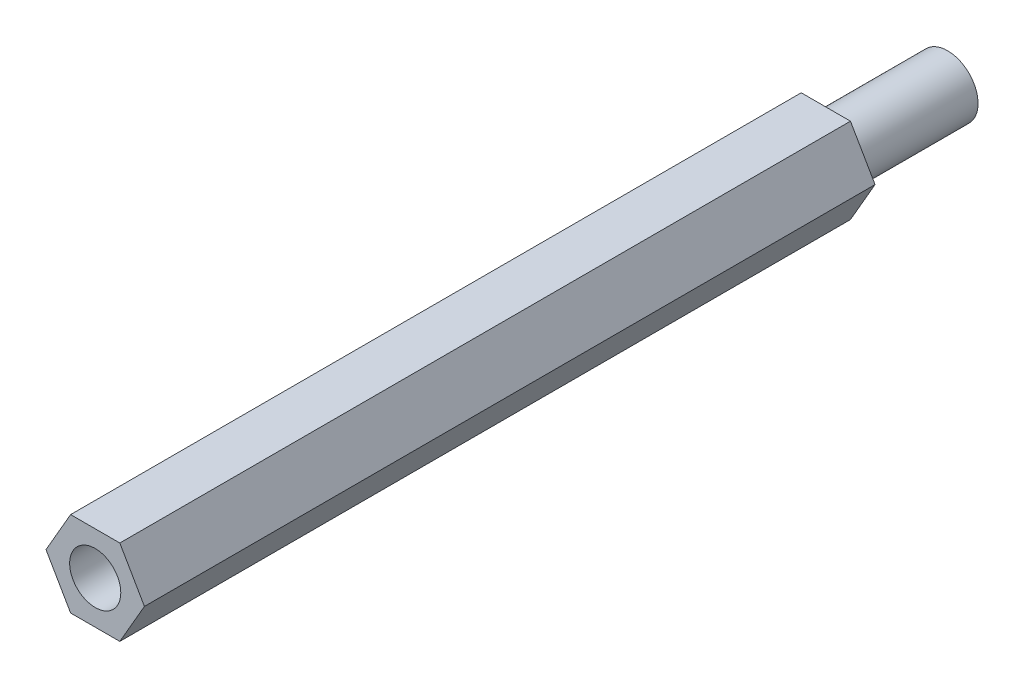
SolidWorks part; units mm, degrees
material "黃銅"
ref_plane "前基準面" through (0, 0, 0) normal (0, 0, 1) x (1, 0, 0)
ref_plane "上基準面" through (0, 0, 0) normal (0, 1, 0) x (1, 0, 0)
ref_plane "右基準面" through (0, 0, 0) normal (1, 0, 0) x (0, 0, -1)
sketch "草圖1" plane through (0, 0, 0) normal (0, 0, 1) x (1, 0, 0)
  line L1 (-2.0207, 3.5) -> (-4.0415, 0)
  line L2 (-4.0415, 0) -> (-2.0207, -3.5)
  line L3 (-2.0207, -3.5) -> (2.0207, -3.5)
  line L4 (2.0207, -3.5) -> (4.0415, 0)
  line L5 (4.0415, 0) -> (2.0207, 3.5)
  line L6 (2.0207, 3.5) -> (-2.0207, 3.5)
  circle A0 centre (0, 0) radius 3.5 construction
  dimension "D1" = 7
extrude "填料-伸長1" add sketch "草圖1" along normal blind 60
sketch "草圖4" plane through (0, 0, 0) normal (0, 0, -1) x (-1, 0, 0)
  circle A0 centre (0, 0) radius 2.5
  dimension "D1" = 5
extrude "填料-伸長2" add sketch "草圖4" along normal blind 10
hole_wizard "M5x0.8 Tapped Hole1" positions "草圖2" profile "草圖3" tap size "M5x0.8" standard "ANSI Metric"
sketch "草圖2" plane through (0, 0, 60) normal (0, 0, 1) x (1, 0, 0)
  point P0 (0, 0)
sketch "草圖3" plane through (0, 0, 60) normal (1, 0, 0) x (0, -1, 0)
  line L0 (0, 0) -> (0, 13.6618)
  line L1 (0, 13.6618) -> (2.1, 12.4)
  line L2 (2.1, 12.4) -> (2.1, 0)
  line L5 (2.1, 0) -> (0, 0)
  line L10 (0, 13.6618) -> (-2.1, 12.4) construction
  line L11 (0, -6.35) -> (0, 107.95) construction
  dimension "螺孔鑽直徑" = 4.2
  dimension "螺孔鑽深度" = 12.4
  dimension "導頭角度" = 118
